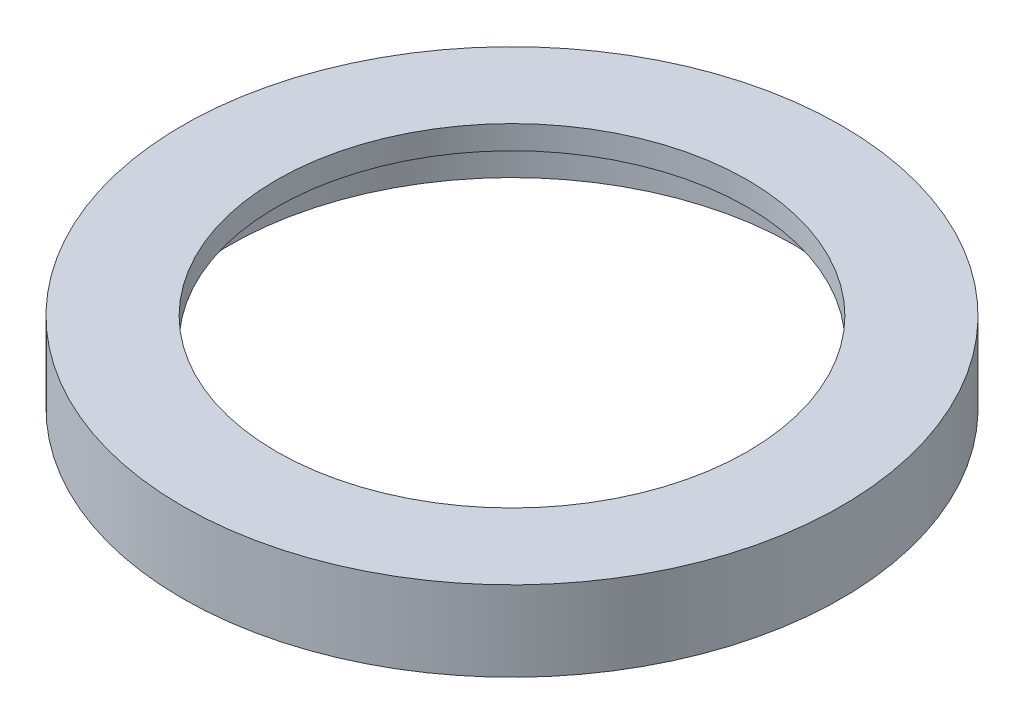
SolidWorks part; units mm, degrees
ref_plane "Front Plane" through (0, 0, 0) normal (0, 0, 1) x (1, 0, 0)
ref_plane "Top Plane" through (0, 0, 0) normal (0, 1, 0) x (1, 0, 0)
ref_plane "Right Plane" through (0, 0, 0) normal (1, 0, 0) x (0, 0, -1)
sketch "Sketch2" plane through (0, 0, 0) normal (0, 1, 0) x (1, 0, 0)
  circle A0 centre (0, 0) radius 350
  circle A1 centre (0, 0) radius 250
  dimension "D1" = 500
  dimension "D2" = 700
extrude "Boss-Extrude1" add sketch "Sketch2" along normal blind 85
sketch "Sketch3" plane through (0, 0, 0) normal (0, -1, 0) x (1, 0, 0)
  circle A0 centre (0, 0) radius 300
  dimension "D1" = 600
extrude "Cut-Extrude1" cut sketch "Sketch3" against normal blind 60
